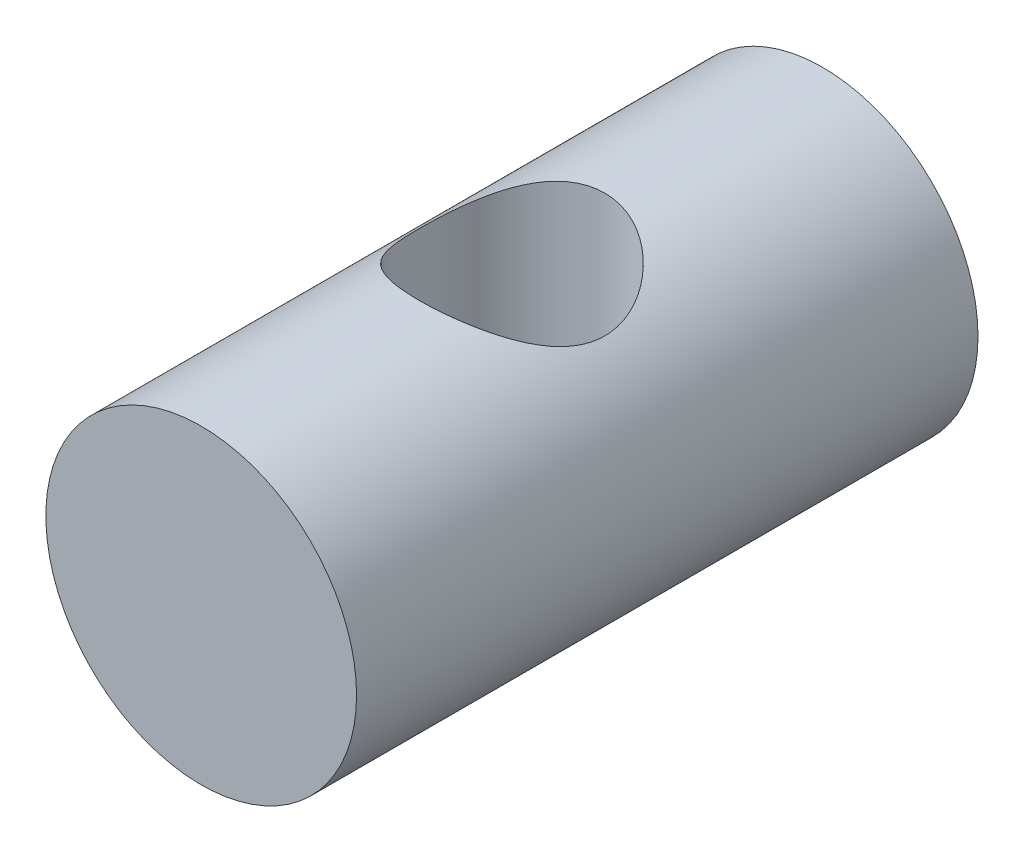
SolidWorks part; units mm, degrees
material "6063-T6"
ref_plane "Front Plane" through (0, 0, 0) normal (0, 0, 1) x (1, 0, 0)
ref_plane "Top Plane" through (0, 0, 0) normal (0, 1, 0) x (1, 0, 0)
ref_plane "Right Plane" through (0, 0, 0) normal (1, 0, 0) x (0, 0, -1)
sketch "Sketch1" plane through (0, 0, 0) normal (0, 0, 1) x (1, 0, 0)
  circle A0 centre (0, 0) radius 3.175
  dimension "D1" = 6.35
extrude "Boss-Extrude1" add sketch "Sketch1" along normal blind 12.7
ref_plane "Plane1" through (0, 0, 6.35) normal (0, 0, 1) x (1, 0, 0)
hole_wizard "#10-24 Tapped Hole2" positions "3DSketch1" profile "Sketch6" tap size "#10-24" standard "ANSI Inch" end condition through all
sketch3d "3DSketch1"
  point P0 (0, 3.175, 6.35)
sketch "Sketch6" plane through (0, 3.175, 6.35) normal (1, 0, 0) x (0, 0, 1)
  line L0 (0, 0) -> (0, 6.35)
  line L1 (0, 6.35) -> (1.8986, 6.35)
  line L2 (1.8986, 6.35) -> (1.8986, 0)
  line L5 (1.8986, 0) -> (0, 0)
  line L11 (0, -6.35) -> (0, 107.95) construction
  dimension "Thru Tap Drill Dia." = 3.7973
  dimension "Thru Tap Drill Depth" = 6.35
cosmetic thread "Hole Thread1" parameters "D2"=4.826
